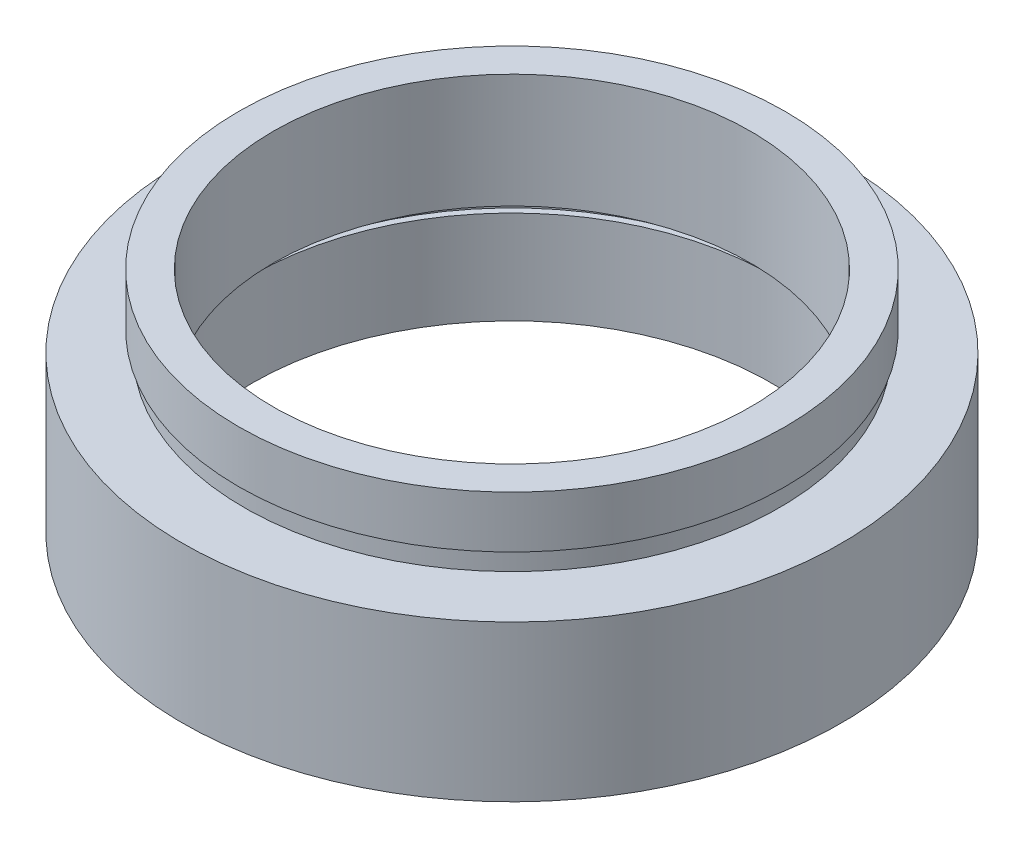
SolidWorks part; units mm, degrees
ref_plane "前视基准面" through (0, 0, 0) normal (0, 0, 1) x (1, 0, 0)
ref_plane "上视基准面" through (0, 0, 0) normal (0, 1, 0) x (1, 0, 0)
ref_plane "右视基准面" through (0, 0, 0) normal (1, 0, 0) x (0, 0, -1)
sketch "草图1" plane through (0, 0, 0) normal (0, 0, 1) x (1, 0, 0)
  line L0 (0, 16.886) -> (0, -24.4878) construction
  line L1 (12.5, 0) -> (12.5, 4.5)
  line L2 (11.5, 5.5) -> (12.8, 5.5)
  line L3 (11.5, 5.5) -> (11.5, 11)
  line L4 (11.5, 11) -> (13.16, 11)
  line L5 (13.16, 11) -> (13.16, 8.5)
  line L6 (13.16, 8.5) -> (12.9, 8.5)
  line L7 (12.9, 8.5) -> (12.9, 7.5)
  line L8 (12.9, 7.5) -> (15.875, 7.5)
  line L9 (15.875, 7.5) -> (15.875, 0)
  line L10 (15.875, 0) -> (12.5, 0)
  line L11 (12.5, 4.5) -> (12.8, 4.5)
  line L12 (12.8, 4.5) -> (12.8, 5.5)
  line L13 (0, 0) -> (3.4668, 0) construction
  point P4 (14.1875, 0)
  dimension "D1" = 11.5
  dimension "D2" = 13.16
  dimension "D3" = 12.9
  dimension "D4" = 12.5
  dimension "D5" = 12.8
  dimension "D6" = 15.875
  dimension "D7" = 11
  dimension "D8" = 7.5
  dimension "D9" = 1
  dimension "D10" = 4.5
  dimension "D11" = 1
revolve "旋转1" add sketch "草图1" angle 360 about L0
cosmetic thread "装饰螺纹线1"
cosmetic thread "装饰螺纹线2"
cosmetic thread "装饰螺纹线3"
